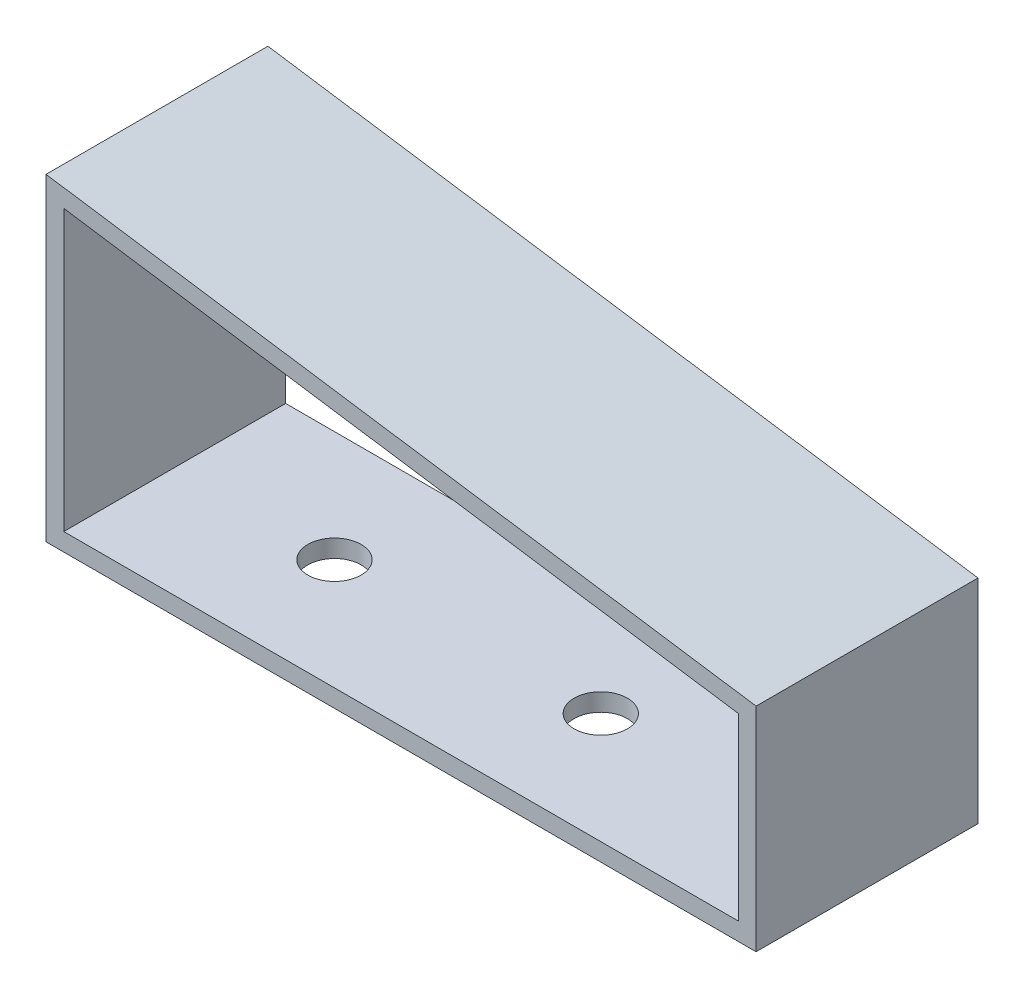
SolidWorks part; units mm, degrees
ref_plane "Front Plane" through (0, 0, 0) normal (0, 0, 1) x (1, 0, 0)
ref_plane "Top Plane" through (0, 0, 0) normal (0, 1, 0) x (1, 0, 0)
ref_plane "Right Plane" through (0, 0, 0) normal (1, 0, 0) x (0, 0, -1)
sketch "Sketch3" plane through (0, 0, 0) normal (0, 0, 1) x (1, 0, 0)
  line L0 (0, 35.8533) -> (0, 0)
  line L1 (0, 0) -> (80, 0)
  line L2 (80, 0) -> (80, 23.9705)
  line L3 (80, 23.9705) -> (0, 35.8533)
  line L4 (2, 33.5343) -> (2, 2)
  line L5 (2, 2) -> (78, 2)
  line L6 (78, 2) -> (78, 22.2456)
  line L7 (78, 22.2456) -> (2, 33.5343)
  dimension "D1" = 98.449
  dimension "D2" = 80
  dimension "D3" = 35.8533
  dimension "D4" = 23.9705
  dimension "D5" = 2
extrude "Boss-Extrude1" add sketch "Sketch3" along normal blind 25
sketch "Sketch4" plane through (0, 0, 0) normal (0, -1, 0) x (1, 0, 0)
  line L0 (0, 25) -> (0, 0) construction
  circle A0 centre (20, 12.5) radius 3
  circle A1 centre (50, 12.5) radius 3
  point P6 (0, 0)
  point P7 (0, 12.5)
  point P8 (0, 0)
  dimension "D3" = 6
  dimension "D1" = 30
  dimension "D2" = 20
extrude "Cut-Extrude1" cut sketch "Sketch4" against normal blind 17
